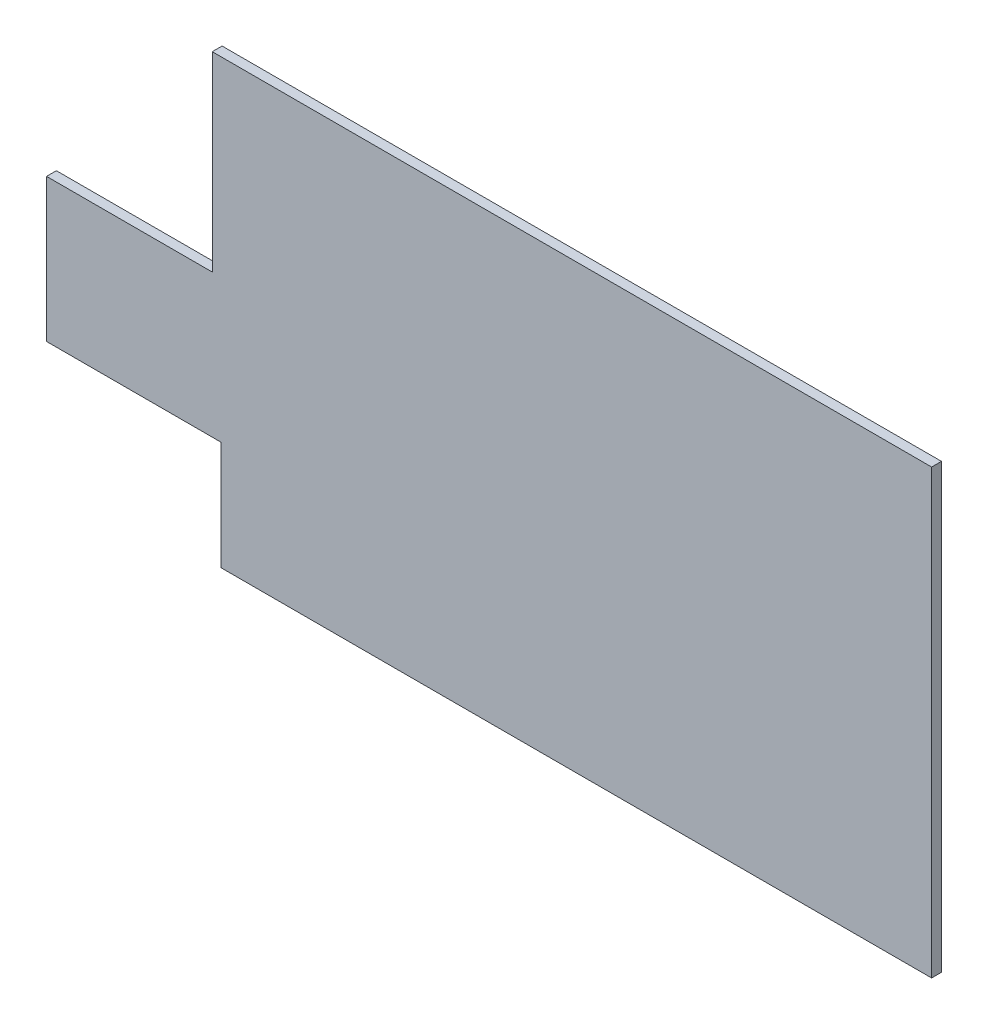
SolidWorks part; units mm, degrees
ref_plane "前视基准面" through (0, 0, 0) normal (0, 0, 1) x (1, 0, 0)
ref_plane "上视基准面" through (0, 0, 0) normal (0, 1, 0) x (1, 0, 0)
ref_plane "右视基准面" through (0, 0, 0) normal (1, 0, 0) x (0, 0, -1)
sketch "草图1" plane through (0, 0, 0) normal (0, 0, 1) x (1, 0, 0)
  line L1 (-90, -45) -> (90, -45)
  line L2 (-90, -45) -> (-90, 45)
  line L3 (-90, 45) -> (90, 45)
  line L4 (90, -45) -> (90, 45)
  line L5 (-90, -45) -> (90, 45) construction
  line L6 (-90, 45) -> (90, -45) construction
  point P0 (0, 0)
  dimension "D1" = 180
  dimension "D2" = 90
extrude "凸台-拉伸1" add sketch "草图1" along normal blind 2
sketch "草图2" plane through (0, 0, 0) normal (0, 0, -1) x (-1, 0, 0)
  line L1 (94.8331, 45.3617) -> (56.3002, 45.3617)
  line L2 (94.8331, 45.3617) -> (94.8331, 6.1888)
  line L3 (94.8331, 6.1888) -> (56.3002, 6.1888)
  line L4 (56.3002, 45.3617) -> (56.3002, 6.1888)
  line L5 (91.2346, -46.8341) -> (54.516, -46.8341)
  line L6 (91.2346, -46.8341) -> (91.2346, -22.8926)
  line L7 (91.2346, -22.8926) -> (54.516, -22.8926)
  line L8 (54.516, -46.8341) -> (54.516, -22.8926)
extrude "切除-拉伸1" cut sketch "草图2" against normal blind 10
